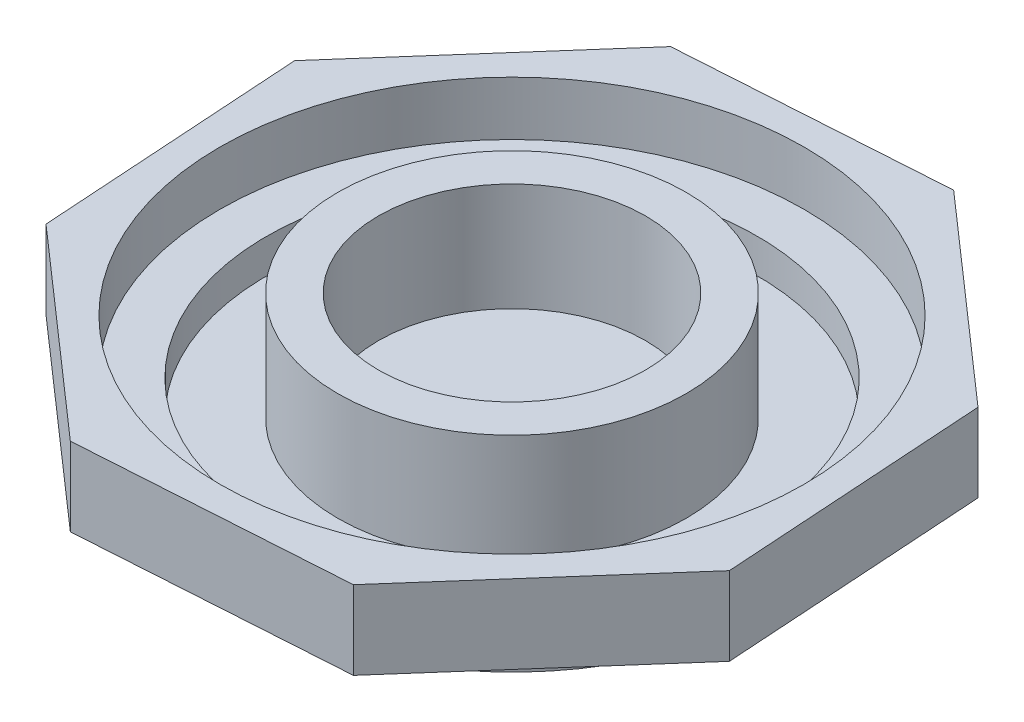
SolidWorks part; units mm, degrees
ref_plane "Front Plane" through (0, 0, 0) normal (0, 0, 1) x (1, 0, 0)
ref_plane "Top Plane" through (0, 0, 0) normal (0, 1, 0) x (1, 0, 0)
ref_plane "Right Plane" through (0, 0, 0) normal (1, 0, 0) x (0, 0, -1)
sketch "Sketch1" plane through (0, 0, 0) normal (0, 1, 0) x (1, 0, 0)
  circle A0 centre (0, 0) radius 13.75
extrude "Boss-Extrude1" add sketch "Sketch1" along normal blind 2
sketch "Sketch2" plane through (0, 2, 0) normal (0, 1, 0) x (1, 0, 0)
  line L1 (16.779, -5.7108) -> (15.9026, 7.8264)
  line L2 (15.9026, 7.8264) -> (5.7108, 16.779)
  line L3 (5.7108, 16.779) -> (-7.8264, 15.9026)
  line L4 (-7.8264, 15.9026) -> (-16.779, 5.7108)
  line L5 (-16.779, 5.7108) -> (-15.9026, -7.8264)
  line L6 (-15.9026, -7.8264) -> (-5.7108, -16.779)
  line L7 (-5.7108, -16.779) -> (7.8264, -15.9026)
  line L8 (7.8264, -15.9026) -> (16.779, -5.7108)
  circle A0 centre (0, 0) radius 16.375 construction
extrude "Boss-Extrude2" add sketch "Sketch2" along normal blind 4
sketch "Sketch3" plane through (0, 6, 0) normal (0, 1, 0) x (1, 0, 0)
  circle A0 centre (0, 0) radius 14.875
extrude "Cut-Extrude1" cut sketch "Sketch3" against normal blind 2.75
sketch "Sketch4" plane through (0, 3.25, 0) normal (0, 1, 0) x (1, 0, 0)
  circle A0 centre (0, 0) radius 12.5
extrude "Cut-Extrude2" cut sketch "Sketch4" against normal blind 1.75
sketch "Sketch5" plane through (0, 1.5, 0) normal (0, 1, 0) x (1, 0, 0)
  circle A0 centre (0, 0) radius 8.875
extrude "Boss-Extrude3" add sketch "Sketch5" along normal blind 5.5
sketch "Sketch6" plane through (0, 7, 0) normal (0, 1, 0) x (1, 0, 0)
  circle A0 centre (0, 0) radius 6.8
extrude "Cut-Extrude3" cut sketch "Sketch6" against normal blind 5.5
